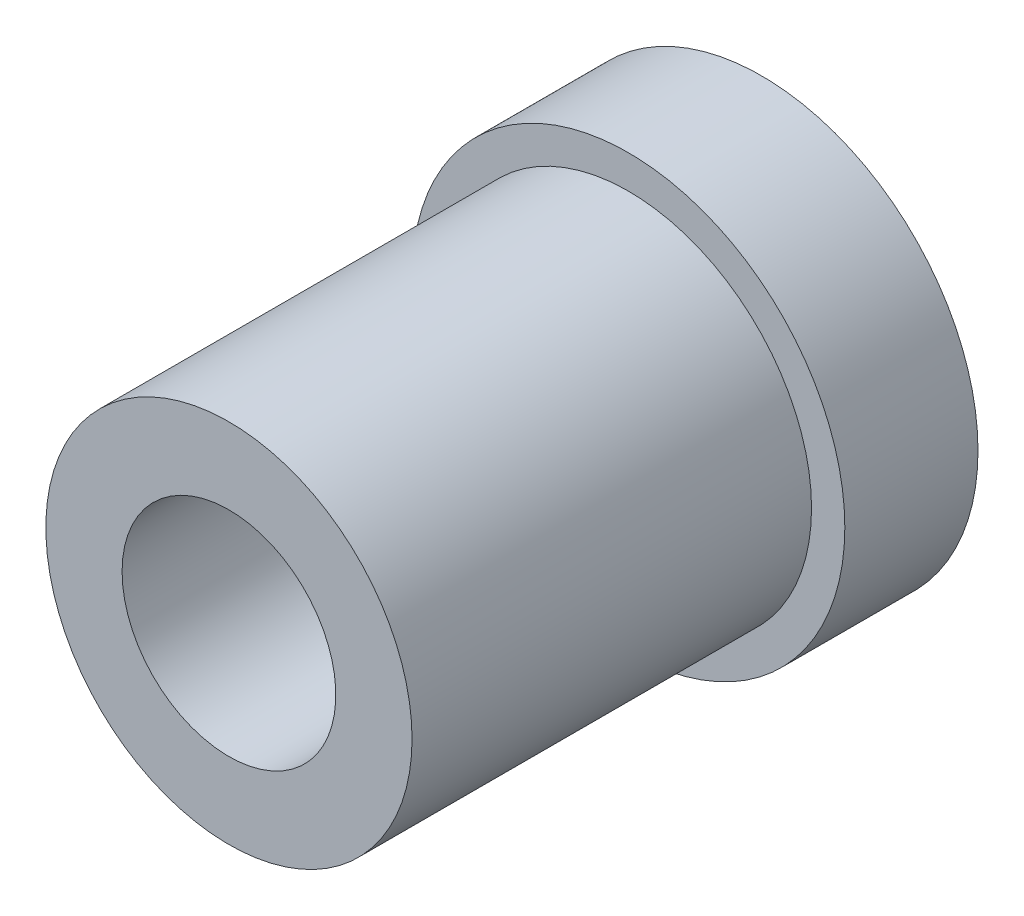
SolidWorks part; units mm, degrees
ref_plane "Plan de face" through (0, 0, 0) normal (0, 0, 1) x (1, 0, 0)
ref_plane "Plan de dessus" through (0, 0, 0) normal (0, 1, 0) x (1, 0, 0)
ref_plane "Plan de droite" through (0, 0, 0) normal (1, 0, 0) x (0, 0, -1)
sketch "Esquisse1" plane through (0, 0, 0) normal (0, 0, 1) x (1, 0, 0)
  circle A0 centre (0, 0) radius 32.5
  dimension "D1" = 65
extrude "Boss.-Extru.1" add sketch "Esquisse1" along normal blind 20
sketch "Esquisse2" plane through (0, 0, 0) normal (0, 0, 1) x (1, 0, 0)
  circle A0 centre (0, 0) radius 27.5
  dimension "D1" = 55
extrude "Boss.-Extru.2" add sketch "Esquisse2" along normal blind 80
sketch "Esquisse3" plane through (0, 0, 0) normal (0, 0, -1) x (-1, 0, 0)
  circle A0 centre (0, 0) radius 16.05
  dimension "D1" = 32.1
extrude "Enlèv. mat.-Extru.1" cut sketch "Esquisse3" against normal through all
